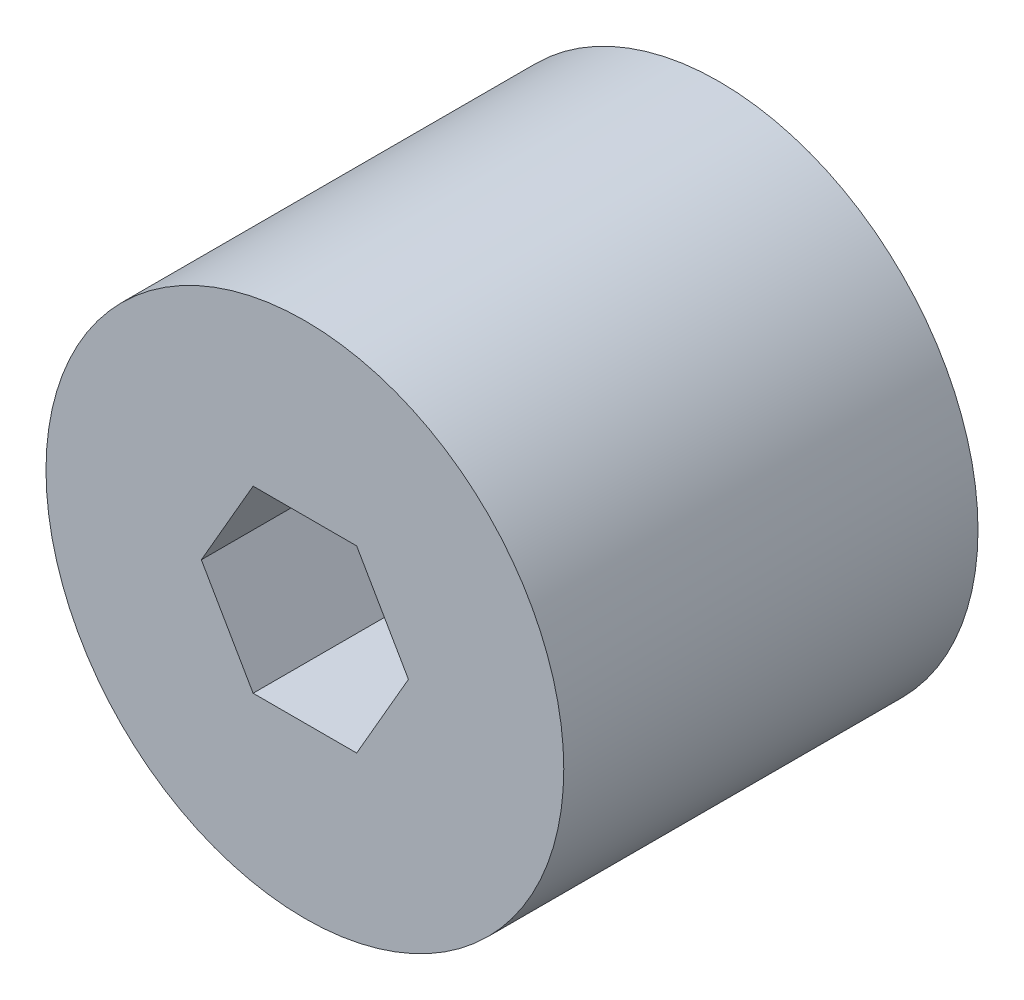
SolidWorks part; units mm, degrees
ref_plane "Front Plane" through (0, 0, 0) normal (0, 0, 1) x (1, 0, 0)
ref_plane "Top Plane" through (0, 0, 0) normal (0, 1, 0) x (1, 0, 0)
ref_plane "Right Plane" through (0, 0, 0) normal (1, 0, 0) x (0, 0, -1)
sketch "Sketch1" plane through (0, 0, 0) normal (0, 0, 1) x (1, 0, 0)
  line L1 (7.62, 0) -> (3.81, 6.5991)
  line L2 (3.81, 6.5991) -> (-3.81, 6.5991)
  line L3 (-3.81, 6.5991) -> (-7.62, 0)
  line L4 (-7.62, 0) -> (-3.81, -6.5991)
  line L5 (-3.81, -6.5991) -> (3.81, -6.5991)
  line L6 (3.81, -6.5991) -> (7.62, 0)
  circle A0 centre (0, 0) radius 15.875
  circle A1 centre (0, 0) radius 6.5991 construction
  dimension "D1" = 31.75
  dimension "D2" = 7.62
extrude "Boss-Extrude1" add sketch "Sketch1" along normal blind 25.4 contours A0
sketch "Sketch3" plane through (0, 0, 25.4) normal (0, 0, 1) x (1, 0, 0)
  line L1 (6.35, 0) -> (3.175, 5.4993)
  line L2 (3.175, 5.4993) -> (-3.175, 5.4993)
  line L3 (-3.175, 5.4993) -> (-6.35, 0)
  line L4 (-6.35, 0) -> (-3.175, -5.4993)
  line L5 (-3.175, -5.4993) -> (3.175, -5.4993)
  line L6 (3.175, -5.4993) -> (6.35, 0)
  circle A0 centre (0, 0) radius 5.4993 construction
  dimension "D1" = 6.35
extrude "Cut-Extrude1" cut sketch "Sketch3" against normal through all
